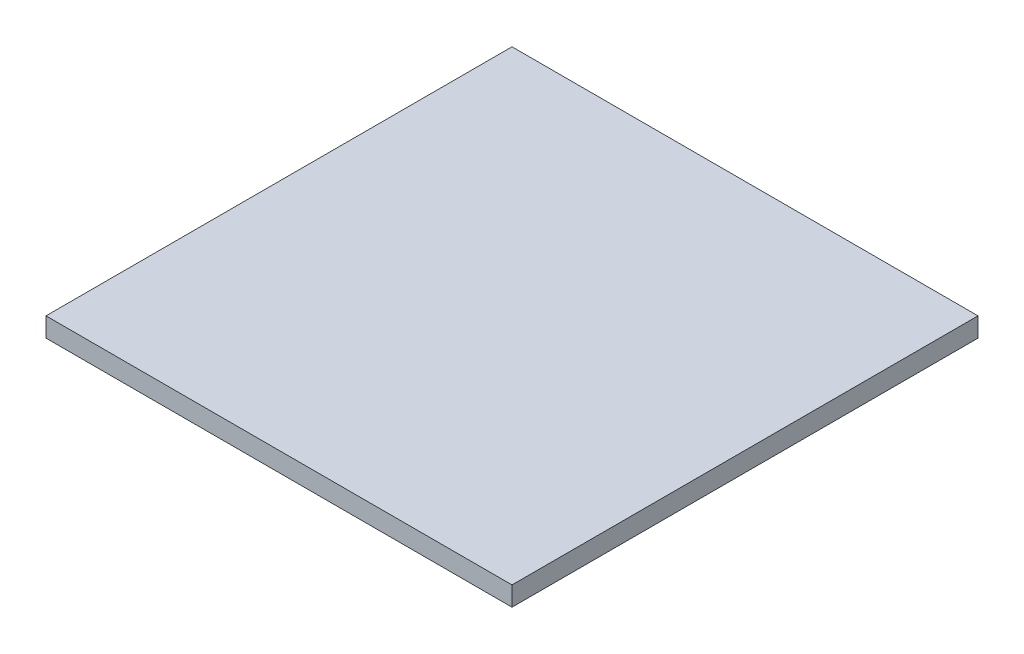
SolidWorks part; units mm, degrees
ref_plane "Front Plane" through (0, 0, 0) normal (0, 0, 1) x (1, 0, 0)
ref_plane "Top Plane" through (0, 0, 0) normal (0, 1, 0) x (1, 0, 0)
ref_plane "Right Plane" through (0, 0, 0) normal (1, 0, 0) x (0, 0, -1)
sketch "Sketch1" plane through (0, 0, 0) normal (0, 0, 1) x (1, 0, 0)
  line L1 (0, 0) -> (1219.2, 0)
  line L2 (0, 0) -> (0, 50.5659)
  line L3 (0, 50.5659) -> (1219.2, 50.5659)
  line L4 (1219.2, 0) -> (1219.2, 50.5659)
  dimension "D1" = 1219.2
extrude "Boss-Extrude1" add sketch "Sketch1" along normal blind 1219.2
